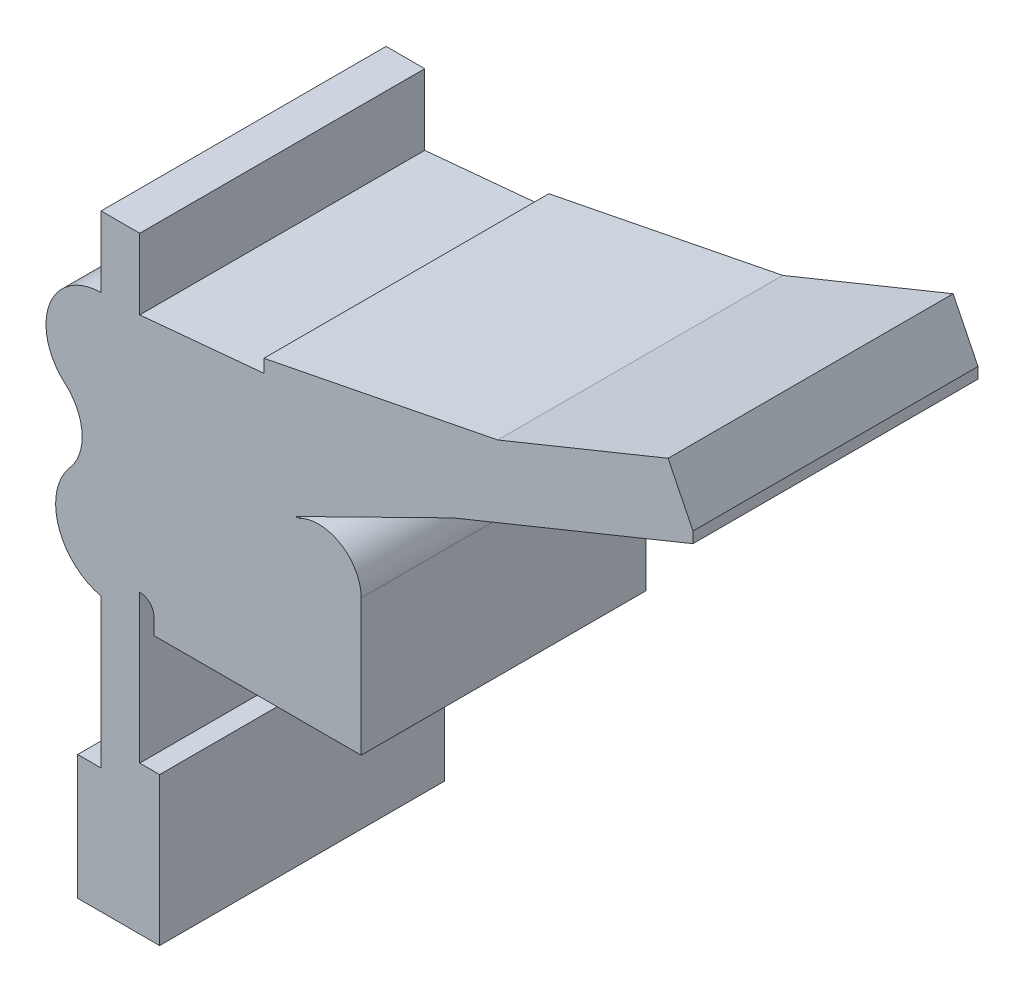
SolidWorks part; units mm, degrees
material "AISI 1020"
ref_plane "Front Plane" through (0, 0, 0) normal (0, 0, 1) x (1, 0, 0)
ref_plane "Top Plane" through (0, 0, 0) normal (0, 1, 0) x (1, 0, 0)
ref_plane "Right Plane" through (0, 0, 0) normal (1, 0, 0) x (0, 0, -1)
sketch "Sketch1" plane through (0, 0, 0) normal (0, 0, 1) x (1, 0, 0)
  line L0 (30.548, 103.7969) -> (152.7402, 103.7969) construction
  line L1 (141.8362, 162.119) -> (136.6868, 172.5787)
  line L2 (136.6868, 172.5787) -> (101.4224, 158.2339)
  line L3 (101.4224, 158.2339) -> (53.0086, 148.6707)
  line L4 (53.0086, 148.6707) -> (53.0086, 145.981)
  line L5 (53.0086, 145.981) -> (27.3075, 143.5902)
  line L6 (27.3075, 143.5902) -> (27.3075, 158.2339)
  line L7 (27.3075, 158.2339) -> (19.3075, 158.2339)
  line L8 (19.3075, 158.2339) -> (19.3075, 143.5902)
  line L9 (19.3075, 89.1696) -> (19.3075, 58.3638)
  line L10 (19.3075, 58.3638) -> (14.4618, 58.3638)
  line L11 (14.4618, 58.3638) -> (14.4618, 32.5787)
  line L12 (14.4618, 32.5787) -> (31.4231, 32.5787)
  line L13 (31.4231, 32.5787) -> (31.4231, 63.2426)
  line L14 (31.4231, 63.2426) -> (27.3075, 63.2426)
  line L15 (27.3075, 63.2426) -> (27.3075, 93.8874)
  line L16 (30.252, 90.9428) -> (30.252, 87.5787)
  line L17 (30.252, 87.5787) -> (73.1512, 87.5787)
  line L18 (73.1512, 87.5787) -> (73.1512, 91.5787)
  line L19 (73.1512, 91.5787) -> (73.1512, 115.776)
  line L20 (59.531, 123.5672) -> (92.1946, 139.6478)
  line L21 (92.1946, 139.6478) -> (141.8362, 159.841)
  line L22 (141.8362, 159.841) -> (141.8362, 162.119)
  line L23 (60.1478, 123.5672) -> (59.531, 123.5672)
  arc A0 (19.3075, 143.5902) -> (11.8362, 123.5672) centre (19.3075, 132.1848) ccw
  arc A1 (11.8362, 123.5672) -> (12.8726, 109.0211) centre (5.0814, 115.776) cw
  arc A2 (12.8726, 109.0211) -> (19.3075, 89.1696) centre (22.0813, 101.0374) ccw
  arc A3 (27.3075, 93.8874) -> (30.252, 90.9428) centre (27.3075, 90.9428) cw
  arc A5 (73.1512, 115.776) -> (60.1478, 123.5672) centre (64.3153, 115.776) ccw
extrude "Boss-Extrude1" add sketch "Sketch1" along normal blind 59
